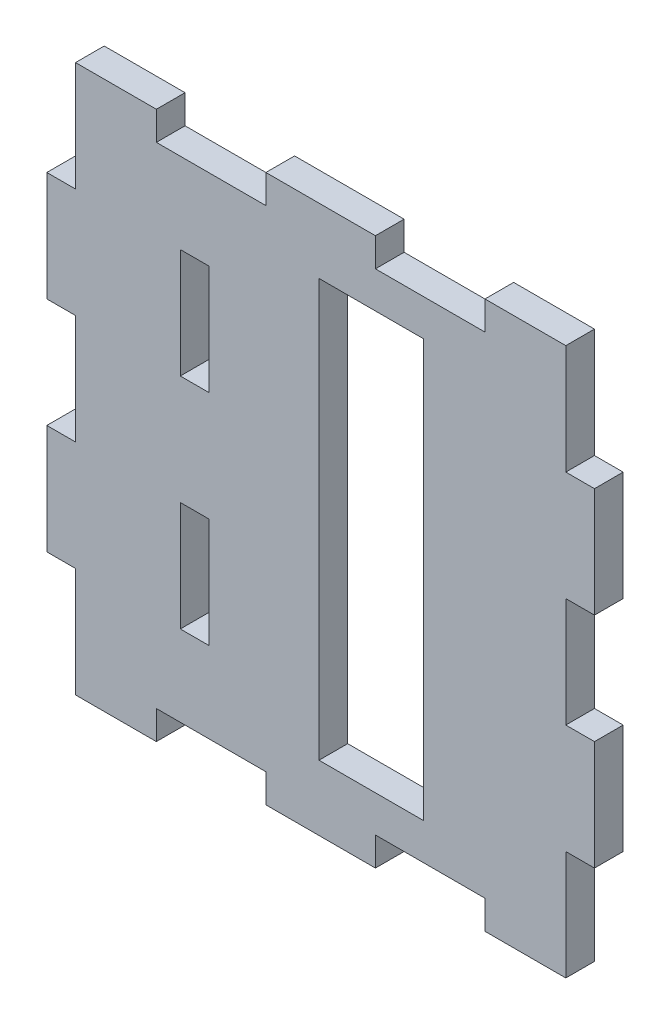
SolidWorks part; units mm, degrees
ref_plane "Alzado" through (0, 0, 0) normal (0, 0, 1) x (1, 0, 0)
ref_plane "Planta" through (0, 0, 0) normal (0, 1, 0) x (1, 0, 0)
ref_plane "Vista lateral" through (0, 0, 0) normal (1, 0, 0) x (0, 0, -1)
sketch "Croquis2" plane through (0, 0, 0) normal (0, 0, 1) x (1, 0, 0)
  line L0 (-47, 50) -> (-47, 31.5)
  line L1 (-47, 31.5) -> (-50, 31.5)
  line L2 (-50, 31.5) -> (-50, 10.5)
  line L3 (-50, 10.5) -> (-47, 10.5)
  line L4 (-47, 10.5) -> (-47, -10.5)
  line L5 (-47, -10.5) -> (-50, -10.5)
  line L6 (-50, -10.5) -> (-50, -31.5)
  line L7 (-50, -31.5) -> (-47, -31.5)
  line L8 (-47, -31.5) -> (-47, -50)
  line L9 (-47, -50) -> (-31.5, -50)
  line L10 (-31.5, -50) -> (-31.5, -47)
  line L11 (-31.5, -47) -> (-10.5, -47)
  line L12 (-10.5, -47) -> (-10.5, -50)
  line L13 (-10.5, -50) -> (10.5, -50)
  line L14 (10.5, -50) -> (10.5, -47)
  line L15 (10.5, -47) -> (31.5, -47)
  line L16 (31.5, -47) -> (31.5, -50)
  line L17 (31.5, -50) -> (47, -50)
  line L18 (47, -50) -> (47, -31.5)
  line L19 (47, -31.5) -> (50, -31.5)
  line L20 (50, -31.5) -> (50, -10.5)
  line L21 (50, -10.5) -> (47, -10.5)
  line L22 (47, -10.5) -> (47, 10.5)
  line L23 (47, 10.5) -> (50, 10.5)
  line L24 (50, 10.5) -> (50, 31.5)
  line L25 (50, 31.5) -> (47, 31.5)
  line L26 (47, 31.5) -> (47, 50)
  line L27 (47, 50) -> (31.5, 50)
  line L28 (31.5, 50) -> (31.5, 47)
  line L29 (31.5, 47) -> (10.5, 47)
  line L30 (10.5, 47) -> (10.5, 50)
  line L31 (10.5, 50) -> (-10.5, 50)
  line L32 (-10.5, 50) -> (-10.5, 47)
  line L33 (-10.5, 47) -> (-31.5, 47)
  line L34 (-31.5, 47) -> (-31.5, 50)
  line L35 (-31.5, 50) -> (-47, 50)
  line L36 (-47, 50) -> (47, -50) construction
  line L37 (47, 50) -> (-47, -50) construction
  line L38 (-47, 0) -> (47, 0) construction
  line L51 (-0.32, -40) -> (19.68, -40)
  line L52 (-0.32, -40) -> (-0.32, 40)
  line L53 (-0.32, 40) -> (19.68, 40)
  line L54 (19.68, -40) -> (19.68, 40)
  line L55 (-26.91, 31.5) -> (-21.41, 31.5)
  line L56 (-26.91, 31.5) -> (-26.91, 10.5)
  line L57 (-26.91, 10.5) -> (-21.41, 10.5)
  line L58 (-21.41, 31.5) -> (-21.41, 10.5)
  line L59 (-21.41, -31.5) -> (-21.41, -10.5)
  line L60 (-26.91, -10.5) -> (-21.41, -10.5)
  line L61 (-26.91, -31.5) -> (-26.91, -10.5)
  line L62 (-26.91, -31.5) -> (-21.41, -31.5)
  point P36 (0, 0)
  point P46 (-24.16, 10.5)
  dimension "D1" = 100
  dimension "D2" = 100
  dimension "D3" = 20
  dimension "D4" = 80
  dimension "D5" = 10
  dimension "D6" = 30.32
  dimension "D7" = 21
  dimension "D8" = 5.5
  dimension "D9" = 21.09
extrude "Saliente-Extruir1" add sketch "Croquis2" along normal blind 5.5
sketch "Croquis3" plane through (-50, 0, 0) normal (-1, 0, 0) x (0, 0, 1)
  line L0 (0, -10.5) -> (0, -31.5) construction
  line L1 (0, -31.5) -> (5.5, -31.5) construction
  line L2 (5.5, -31.5) -> (5.5, -10.5) construction
  line L3 (5.5, -10.5) -> (0, -10.5) construction
  line L4 (0, 31.5) -> (0, 10.5) construction
  line L5 (0, 10.5) -> (5.5, 10.5) construction
  line L6 (5.5, 10.5) -> (5.5, 31.5) construction
  line L7 (5.5, 31.5) -> (0, 31.5) construction
  line L8 (0, -10.5) -> (0, -31.5)
  line L9 (0, -31.5) -> (5.5, -31.5)
  line L10 (5.5, -31.5) -> (5.5, -10.5)
  line L11 (5.5, -10.5) -> (0, -10.5)
  line L12 (0, 31.5) -> (0, 10.5)
  line L13 (0, 10.5) -> (5.5, 10.5)
  line L14 (5.5, 10.5) -> (5.5, 31.5)
  line L15 (5.5, 31.5) -> (0, 31.5)
extrude "Saliente-Extruir2" add sketch "Croquis3" along normal blind 2.5
sketch "Croquis4" plane through (0, 50, 0) normal (0, 1, 0) x (1, 0, 0)
  line L0 (47, 0) -> (31.5, 0) construction
  line L1 (31.5, 0) -> (31.5, -5.5) construction
  line L2 (31.5, -5.5) -> (47, -5.5) construction
  line L3 (47, -5.5) -> (47, 0) construction
  line L4 (10.5, 0) -> (-10.5, 0) construction
  line L5 (-10.5, 0) -> (-10.5, -5.5) construction
  line L6 (-10.5, -5.5) -> (10.5, -5.5) construction
  line L7 (10.5, -5.5) -> (10.5, 0) construction
  line L8 (-31.5, 0) -> (-47, 0) construction
  line L9 (-47, 0) -> (-47, -5.5) construction
  line L10 (-47, -5.5) -> (-31.5, -5.5) construction
  line L11 (-31.5, -5.5) -> (-31.5, 0) construction
  line L12 (47, 0) -> (31.5, 0)
  line L13 (31.5, 0) -> (31.5, -5.5)
  line L14 (31.5, -5.5) -> (47, -5.5)
  line L15 (47, -5.5) -> (47, 0)
  line L16 (10.5, 0) -> (-10.5, 0)
  line L17 (-10.5, 0) -> (-10.5, -5.5)
  line L18 (-10.5, -5.5) -> (10.5, -5.5)
  line L19 (10.5, -5.5) -> (10.5, 0)
  line L20 (-31.5, 0) -> (-47, 0)
  line L21 (-47, 0) -> (-47, -5.5)
  line L22 (-47, -5.5) -> (-31.5, -5.5)
  line L23 (-31.5, -5.5) -> (-31.5, 0)
extrude "Saliente-Extruir3" add sketch "Croquis4" along normal blind 2.5
sketch "Croquis5" plane through (50, 0, 0) normal (1, 0, 0) x (0, 0, -1)
  line L0 (0, -31.5) -> (0, -10.5) construction
  line L1 (0, -10.5) -> (-5.5, -10.5) construction
  line L2 (-5.5, -10.5) -> (-5.5, -31.5) construction
  line L3 (-5.5, -31.5) -> (0, -31.5) construction
  line L4 (0, 10.5) -> (0, 31.5) construction
  line L5 (0, 31.5) -> (-5.5, 31.5) construction
  line L6 (-5.5, 31.5) -> (-5.5, 10.5) construction
  line L7 (-5.5, 10.5) -> (0, 10.5) construction
  line L8 (0, -31.5) -> (0, -10.5)
  line L9 (0, -10.5) -> (-5.5, -10.5)
  line L10 (-5.5, -10.5) -> (-5.5, -31.5)
  line L11 (-5.5, -31.5) -> (0, -31.5)
  line L12 (0, 10.5) -> (0, 31.5)
  line L13 (0, 31.5) -> (-5.5, 31.5)
  line L14 (-5.5, 31.5) -> (-5.5, 10.5)
  line L15 (-5.5, 10.5) -> (0, 10.5)
extrude "Saliente-Extruir4" add sketch "Croquis5" along normal blind 2.5
sketch "Croquis6" plane through (0, -50, 0) normal (0, -1, 0) x (1, 0, 0)
  line L0 (31.5, 0) -> (47, 0) construction
  line L1 (47, 0) -> (47, 5.5) construction
  line L2 (47, 5.5) -> (31.5, 5.5) construction
  line L3 (31.5, 5.5) -> (31.5, 0) construction
  line L4 (-10.5, 0) -> (10.5, 0) construction
  line L5 (10.5, 0) -> (10.5, 5.5) construction
  line L6 (10.5, 5.5) -> (-10.5, 5.5) construction
  line L7 (-10.5, 5.5) -> (-10.5, 0) construction
  line L8 (-47, 0) -> (-31.5, 0) construction
  line L9 (-31.5, 0) -> (-31.5, 5.5) construction
  line L10 (-31.5, 5.5) -> (-47, 5.5) construction
  line L11 (-47, 5.5) -> (-47, 0) construction
  line L12 (31.5, 0) -> (47, 0)
  line L13 (47, 0) -> (47, 5.5)
  line L14 (47, 5.5) -> (31.5, 5.5)
  line L15 (31.5, 5.5) -> (31.5, 0)
  line L16 (-10.5, 0) -> (10.5, 0)
  line L17 (10.5, 0) -> (10.5, 5.5)
  line L18 (10.5, 5.5) -> (-10.5, 5.5)
  line L19 (-10.5, 5.5) -> (-10.5, 0)
  line L20 (-47, 0) -> (-31.5, 0)
  line L21 (-31.5, 0) -> (-31.5, 5.5)
  line L22 (-31.5, 5.5) -> (-47, 5.5)
  line L23 (-47, 5.5) -> (-47, 0)
extrude "Saliente-Extruir5" add sketch "Croquis6" along normal blind 2.5
